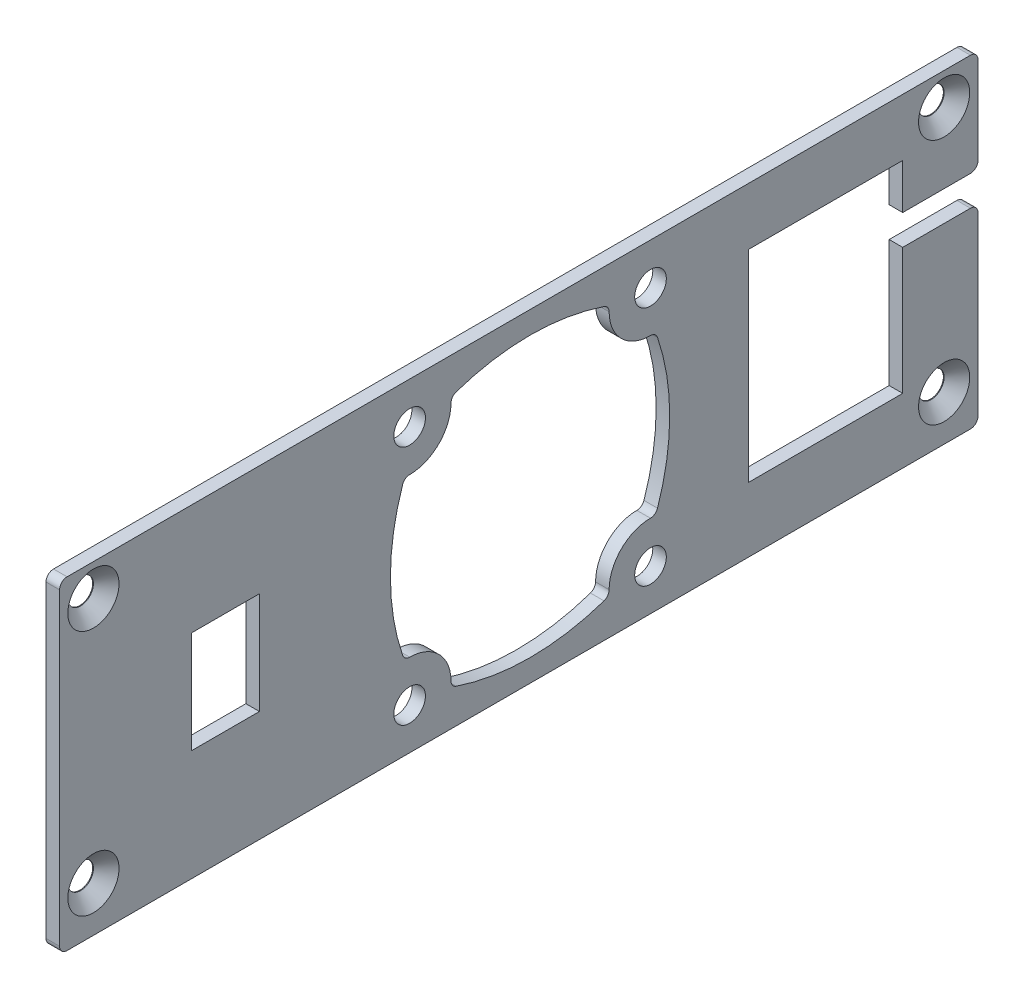
SolidWorks part; units mm, degrees
ref_plane "Front Plane" through (0, 0, 0) normal (0, 0, 1) x (1, 0, 0)
ref_plane "Top Plane" through (0, 0, 0) normal (0, 1, 0) x (1, 0, 0)
ref_plane "Right Plane" through (0, 0, 0) normal (1, 0, 0) x (0, 0, -1)
sketch "Sketch1" plane through (0, 0, 0) normal (1, 0, 0) x (0, 0, -1)
  line L1 (61, 21.5) -> (-61, 21.5)
  line L2 (61, 21.5) -> (61, -21.5)
  line L3 (61, -21.5) -> (-61, -21.5)
  line L4 (-61, 21.5) -> (-61, -21.5)
  line L5 (61, 21.5) -> (-61, -21.5) construction
  line L6 (61, -21.5) -> (-61, 21.5) construction
  point P0 (0, 0)
  dimension "D1" = 43
  dimension "D2" = 122
extrude "Boss-Extrude1" add sketch "Sketch1" along normal blind 1.8
sketch "Sketch2" plane through (1.8, 0, 0) normal (1, 0, 0) x (0, 0, -1)
  line L0 (-61, 21.5) -> (-61, -21.5) construction
  line L1 (-43.5, -6.77) -> (-34.45, -6.77)
  line L2 (-43.5, -6.77) -> (-43.5, 6.78)
  line L3 (-43.5, 6.78) -> (-34.45, 6.78)
  line L4 (-34.45, -6.77) -> (-34.45, 6.78)
  line L5 (-43.5, -6.77) -> (-34.45, 6.78) construction
  line L6 (-43.5, 6.78) -> (-34.45, -6.77) construction
  line L7 (-61, -21.5) -> (61, -21.5) construction
  point P0 (-38.975, 0.005)
  dimension "D1" = 17.5
  dimension "D2" = 14.73
  dimension "D3" = 9.05
  dimension "D4" = 13.55
extrude "Cut-Extrude1" cut sketch "Sketch2" against normal blind 1.8 contours L2 L3 L4 L1
hole_wizard "CSK for M3 Countersunk Flat Head Screw1" positions "Sketch4" profile "Sketch3" countersink size "M3" standard "DIN" end condition through all
sketch "Sketch4" plane through (1.8, 0, 0) normal (1, 0, 0) x (0, 0, -1)
  line L0 (-61, 21.5) -> (-61, -21.5) construction
  line L1 (-61, -21.5) -> (61, -21.5) construction
  line L2 (61, 21.5) -> (-61, 21.5) construction
  line L3 (61, -21.5) -> (61, 21.5) construction
  point P0 (-56.5, -15.5)
  point P7 (-56.5, 17.25)
  point P12 (56.5, 17.25)
  point P14 (56.5, -15.5)
  dimension "D1" = 4.5
  dimension "D2" = 6
  dimension "D3" = 4.25
  dimension "D4" = 4.5
  dimension "D5" = 4.5
  dimension "D6" = 4.5
  dimension "D7" = 6
  dimension "D8" = 4.25
sketch "Sketch3" plane through (1.8, -15.5, 56.5) normal (0, 1, 0) x (0, 0, -1)
  line L0 (0, 0) -> (0, 1.8)
  line L1 (0, 1.8) -> (1.7, 1.8)
  line L2 (1.7, 1.8) -> (1.7, 1.7)
  line L3 (1.7, 1.7) -> (3.4, 0)
  line L5 (3.4, 0) -> (0, 0)
  line L6 (-1.7, 1.7) -> (-3.4, 0) construction
  line L11 (0, -6.35) -> (0, 107.95) construction
  dimension "Thru Hole Dia." = 3.4
  dimension "Thru Hole Depth" = 1.8
  dimension "Near C'Sink Dia." = 6.8
  dimension "Near C'Sink Angle" = 90
sketch "Sketch5" plane through (1.8, 0, 0) normal (1, 0, 0) x (0, 0, -1)
  line L0 (61, 21.5) -> (-61, 21.5) construction
  line L1 (30.5, -12.9) -> (51, -12.9)
  line L2 (30.5, -12.9) -> (30.5, 13.9)
  line L3 (30.5, 13.9) -> (51, 13.9)
  line L4 (51, -12.9) -> (51, 3.9)
  line L5 (30.5, -12.9) -> (51, 13.9) construction
  line L6 (30.5, 13.9) -> (51, -12.9) construction
  line L7 (61, -21.5) -> (61, 21.5) construction
  line L8 (51, 7.9) -> (61, 7.9)
  line L9 (51, 3.9) -> (61, 3.9)
  line L10 (61, 7.9) -> (61, 3.9)
  line L11 (51, 7.9) -> (51, 13.9)
  point P0 (40.75, 0.5)
  dimension "D1" = 7.6
  dimension "D2" = 10
  dimension "D3" = 20.5
  dimension "D4" = 26.8
  dimension "D5" = 6
  dimension "D6" = 4
extrude "Cut-Extrude2" cut sketch "Sketch5" against normal blind 1.8
fillet "Fillet1" radius 1 6 edges at (0.9, 21.5, -61) (0.9, 7.9, -61) (0.9, 3.9, -61) (0.9, -21.5, -61) (0.9, -21.5, 61) (0.9, 21.5, 61)
hole_wizard "Ø4.2 (4.2) Diameter Hole1" positions "Sketch7" profile "Sketch6" hole size "Ø4.2" standard "DIN"
sketch "Sketch7" plane through (1.8, 0, 0) normal (1, 0, 0) x (0, 0, -1)
  line L0 (-60, -21.5) -> (60, -21.5) construction
  line L1 (-61, 20.5) -> (-61, -20.5) construction
  point P0 (-14.5, 16)
  point P2 (17.5, 16)
  point P4 (17.5, -16)
  point P6 (-14.5, -16)
  dimension "D1" = 5.5
  dimension "D2" = 5.5
  dimension "D3" = 32
  dimension "D4" = 32
  dimension "D5" = 46.5
  dimension "D6" = 46.5
  dimension "D7" = 32
  dimension "D8" = 32
sketch "Sketch6" plane through (1.8, 16, 14.5) normal (0, 1, 0) x (0, 0, -1)
  line L0 (0, 0) -> (0, 3.0618)
  line L1 (0, 3.0618) -> (2.1, 1.8)
  line L2 (2.1, 1.8) -> (2.1, 0)
  line L5 (2.1, 0) -> (0, 0)
  line L10 (0, 3.0618) -> (-2.1, 1.8) construction
  line L11 (0, -6.35) -> (0, 107.95) construction
  dimension "Hole Dia." = 4.2
  dimension "Hole Depth" = 1.8
  dimension "Drill Angle" = 118
sketch "Sketch8" plane through (1.8, 0, 0) normal (1, 0, 0) x (0, 0, -1)
  arc A0 (12, 15.9842) -> (17.4842, 10.5) centre (17.5, 16) ccw
  arc A1 (-8.3215, -16.9282) -> (11.3215, -16.9282) centre (1.5, 12) ccw
  arc A2 (18.4282, -9.8215) -> (18.4282, 9.8215) centre (-10.5, 0) ccw
  arc A3 (17.4842, -10.5) -> (12, -15.9842) centre (17.5, -16) ccw
  arc A4 (-9, -15.9842) -> (-14.4842, -10.5) centre (-14.5, -16) ccw
  arc A5 (-15.4282, 9.8215) -> (-15.4282, -9.8215) centre (13.5, 0) ccw
  arc A6 (-14.4842, 10.5) -> (-9, 15.9842) centre (-14.5, 16) ccw
  arc A7 (11.3215, 16.9282) -> (-8.3215, 16.9282) centre (1.5, -12) ccw
  arc A8 (-15.4282, -9.8215) -> (-14.4842, -10.5) centre (-14.4813, -9.5) ccw
  arc A9 (-14.4842, 10.5) -> (-15.4282, 9.8215) centre (-14.4813, 9.5) ccw
  arc A10 (-8.3215, 16.9282) -> (-9, 15.9842) centre (-8, 15.9813) ccw
  arc A11 (12, 15.9842) -> (11.3215, 16.9282) centre (11, 15.9813) ccw
  arc A12 (18.4282, 9.8215) -> (17.4842, 10.5) centre (17.4813, 9.5) ccw
  arc A13 (17.4842, -10.5) -> (18.4282, -9.8215) centre (17.4813, -9.5) ccw
  arc A14 (11.3215, -16.9282) -> (12, -15.9842) centre (11, -15.9813) ccw
  arc A15 (-9, -15.9842) -> (-8.3215, -16.9282) centre (-8, -15.9813) ccw
  point P4 (1.5, 16)
  point P5 (1.5, -36.8705)
  dimension "D1" = 1
  dimension "D2" = 1
  dimension "D3" = 1
  dimension "D4" = 1
  dimension "D5" = 1
  dimension "D6" = 1
  dimension "D7" = 1
  dimension "D8" = 1
extrude "Cut-Extrude3" cut sketch "Sketch8" against normal blind 1.8
